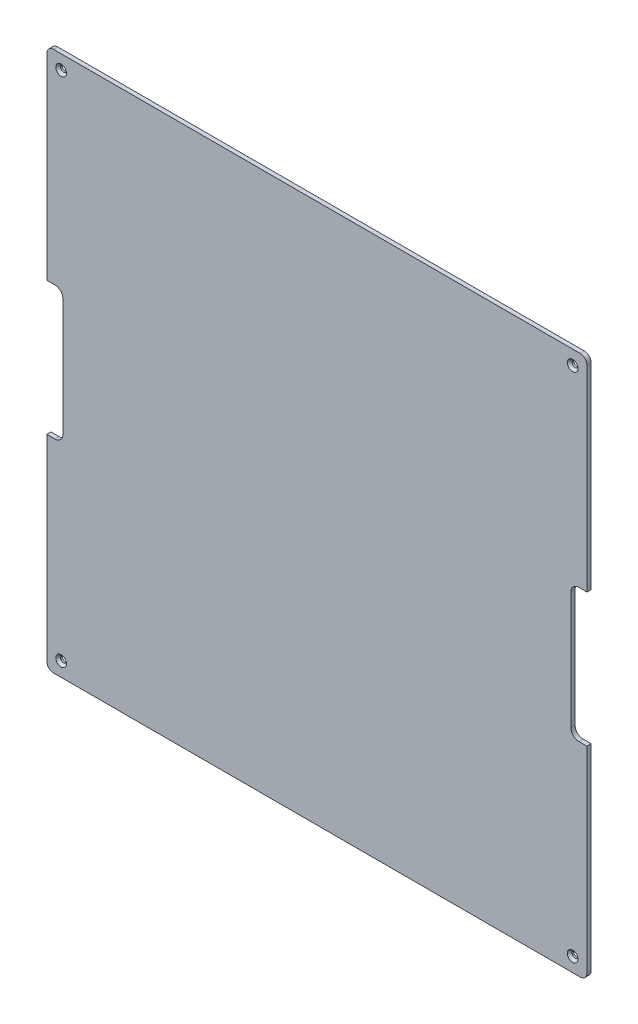
SolidWorks part; units mm, degrees
ref_plane "Front Plane" through (0, 0, 0) normal (0, 0, 1) x (1, 0, 0)
ref_plane "Top Plane" through (0, 0, 0) normal (0, 1, 0) x (1, 0, 0)
ref_plane "Right Plane" through (0, 0, 0) normal (1, 0, 0) x (0, 0, -1)
sketch "Sketch1" plane through (0, 0, 0) normal (0, 0, 1) x (1, 0, 0)
  line L0 (3.3022, 206.6978) -> (3.3022, 129.9978)
  line L1 (3.3022, 3.2978) -> (206.7022, 3.2978)
  line L2 (206.7022, 3.2978) -> (206.7022, 79.9978)
  line L3 (206.7022, 206.6978) -> (3.3022, 206.6978)
  line L4 (206.7022, 129.9978) -> (206.7022, 206.6978)
  line L5 (3.3022, 129.9978) -> (9.8222, 129.9978)
  line L7 (3.3022, 79.9978) -> (9.8222, 79.9978)
  line L8 (9.8222, 129.9978) -> (9.8222, 79.9978)
  line L9 (206.7022, 129.9978) -> (200.1822, 129.9978)
  line L11 (206.7022, 79.9978) -> (200.1822, 79.9978)
  line L12 (200.1822, 129.9978) -> (200.1822, 79.9978)
  line L13 (3.3022, 79.9978) -> (3.3022, 3.2978)
  dimension "D1" = 203.4
  dimension "D2" = 203.4
  dimension "D3" = 6.52
  dimension "D4" = 50
  dimension "D5" = 76.7
  dimension "D6" = 76.7
extrude "Boss-Extrude1" add sketch "Sketch1" along normal blind 1.5748
hole_wizard "CSK for M2 Flat Head Machine Screw1" positions "Sketch2" profile "Sketch3" countersink size "M2" standard "ANSI Metric" end condition up to next
sketch "Sketch2" plane through (0, 0, 1.5748) normal (0, 0, 1) x (1, 0, 0)
  point P0 (200.8489, 9.1511)
  point P2 (9.1511, 9.1511)
  point P4 (200.8489, 200.8489)
  point P6 (9.1511, 200.8489)
sketch "Sketch3" plane through (200.8489, 9.1511, 1.5748) normal (1, 0, 0) x (0, -1, 0)
  line L0 (0, 0) -> (0, 1.5748)
  line L1 (0, 1.5748) -> (1.1, 1.5748)
  line L2 (1.1, 1.5748) -> (1.1, 0.9)
  line L3 (1.1, 0.9) -> (2, 0)
  line L5 (2, 0) -> (0, 0)
  line L6 (-1.1, 0.9) -> (-2, 0) construction
  line L11 (0, -6.35) -> (0, 107.95) construction
  dimension "Thru Hole Dia." = 2.2
  dimension "Thru Hole Depth" = 1.5748
  dimension "Near C'Sink Dia." = 4
  dimension "Near C'Sink Angle" = 90
fillet "Fillet1" radius 3 8 edges at (200.1822, 129.9978, 0.7874) (200.1822, 79.9978, 0.7874) (9.8222, 129.9978, 0.7874) (9.8222, 79.9978, 0.7874) (3.3022, 3.2978, 0.7874) (206.7022, 3.2978, 0.7874) (206.7022, 206.6978, 0.7874) (3.3022, 206.6978, 0.7874)
sketch "Sketch4" plane through (0, 0, 1.5748) normal (0, 0, 1) x (1, 0, 0)
  line L0 (3.3022, 79.9978) -> (3.3022, 6.2978) construction
  line L1 (6.3022, 3.7978) -> (203.7022, 3.7978)
  line L2 (206.2022, 6.2978) -> (206.2022, 203.6978)
  line L3 (203.7022, 206.1978) -> (6.3022, 206.1978)
  line L4 (3.8022, 203.6978) -> (3.8022, 6.2978)
  line L12 (3.3022, 79.9978) -> (3.3022, 6.2978)
  line L13 (6.3022, 3.2978) -> (203.7022, 3.2978)
  line L14 (206.7022, 6.2978) -> (206.7022, 79.9978)
  line L15 (206.7022, 79.9978) -> (203.1822, 79.9978)
  line L16 (200.1822, 82.9978) -> (200.1822, 126.9978)
  line L17 (203.1822, 129.9978) -> (206.7022, 129.9978)
  line L18 (206.7022, 129.9978) -> (206.7022, 203.6978)
  line L19 (203.7022, 206.6978) -> (6.3022, 206.6978)
  line L20 (3.3022, 203.6978) -> (3.3022, 129.9978)
  line L21 (3.3022, 129.9978) -> (6.8222, 129.9978)
  line L22 (9.8222, 126.9978) -> (9.8222, 82.9978)
  line L23 (6.8222, 79.9978) -> (3.3022, 79.9978)
  line L25 (6.3022, 3.2978) -> (203.7022, 3.2978)
  line L30 (206.7022, 6.2978) -> (206.7022, 203.6978)
  line L31 (203.7022, 206.6978) -> (6.3022, 206.6978)
  line L32 (3.3022, 203.6978) -> (3.3022, 6.2978)
  arc A0 (203.7022, 3.7978) -> (206.2022, 6.2978) centre (203.7022, 6.2978) ccw
  arc A1 (206.2022, 203.6978) -> (203.7022, 206.1978) centre (203.7022, 203.6978) ccw
  arc A2 (6.3022, 206.1978) -> (3.8022, 203.6978) centre (6.3022, 203.6978) ccw
  arc A3 (3.8022, 6.2978) -> (6.3022, 3.7978) centre (6.3022, 6.2978) ccw
  arc A8 (3.3022, 6.2978) -> (6.3022, 3.2978) centre (6.3022, 6.2978) ccw
  arc A9 (203.7022, 3.2978) -> (206.7022, 6.2978) centre (203.7022, 6.2978) ccw
  arc A10 (200.1822, 82.9978) -> (203.1822, 79.9978) centre (203.1822, 82.9978) ccw
  arc A11 (203.1822, 129.9978) -> (200.1822, 126.9978) centre (203.1822, 126.9978) ccw
  arc A12 (206.7022, 203.6978) -> (203.7022, 206.6978) centre (203.7022, 203.6978) ccw
  arc A13 (6.3022, 206.6978) -> (3.3022, 203.6978) centre (6.3022, 203.6978) ccw
  arc A14 (9.8222, 126.9978) -> (6.8222, 129.9978) centre (6.8222, 126.9978) ccw
  arc A15 (6.8222, 79.9978) -> (9.8222, 82.9978) centre (6.8222, 82.9978) ccw
  arc A16 (3.3022, 6.2978) -> (6.3022, 3.2978) centre (6.3022, 6.2978) ccw
  arc A17 (203.7022, 3.2978) -> (206.7022, 6.2978) centre (203.7022, 6.2978) ccw
  arc A20 (206.7022, 203.6978) -> (203.7022, 206.6978) centre (203.7022, 203.6978) ccw
  arc A21 (6.3022, 206.6978) -> (3.3022, 203.6978) centre (6.3022, 203.6978) ccw
  dimension "D1" = 0
  dimension "D2" = 0.5
extrude "Cut-Extrude1" cut sketch "Sketch4" against normal up to next
